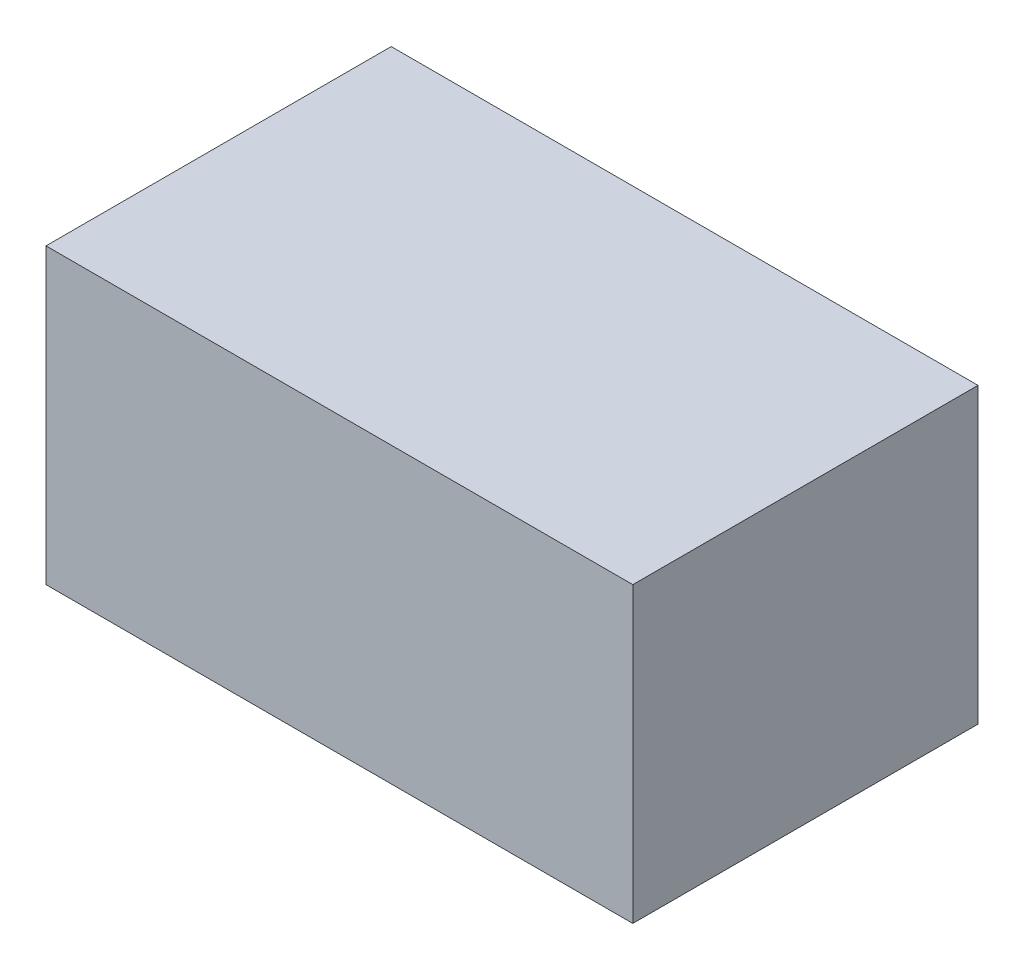
SolidWorks part; units mm, degrees
material "1060-H16"
ref_plane "Front Plane" through (0, 0, 0) normal (0, 0, 1) x (1, 0, 0)
ref_plane "Top Plane" through (0, 0, 0) normal (0, 1, 0) x (1, 0, 0)
ref_plane "Right Plane" through (0, 0, 0) normal (1, 0, 0) x (0, 0, -1)
sketch "Sketch1" plane through (0, 0, 0) normal (0, 1, 0) x (1, 0, 0)
  line L1 (-0.17, -0.1) -> (0.17, -0.1)
  line L2 (-0.17, -0.1) -> (-0.17, 0.1)
  line L3 (-0.17, 0.1) -> (0.17, 0.1)
  line L4 (0.17, -0.1) -> (0.17, 0.1)
  line L5 (-0.17, -0.1) -> (0.17, 0.1) construction
  line L6 (-0.17, 0.1) -> (0.17, -0.1) construction
  point P0 (0, 0)
  dimension "D1" = 0.34
  dimension "D2" = 0.2
extrude "Boss-Extrude1" add sketch "Sketch1" along normal blind 0.17
